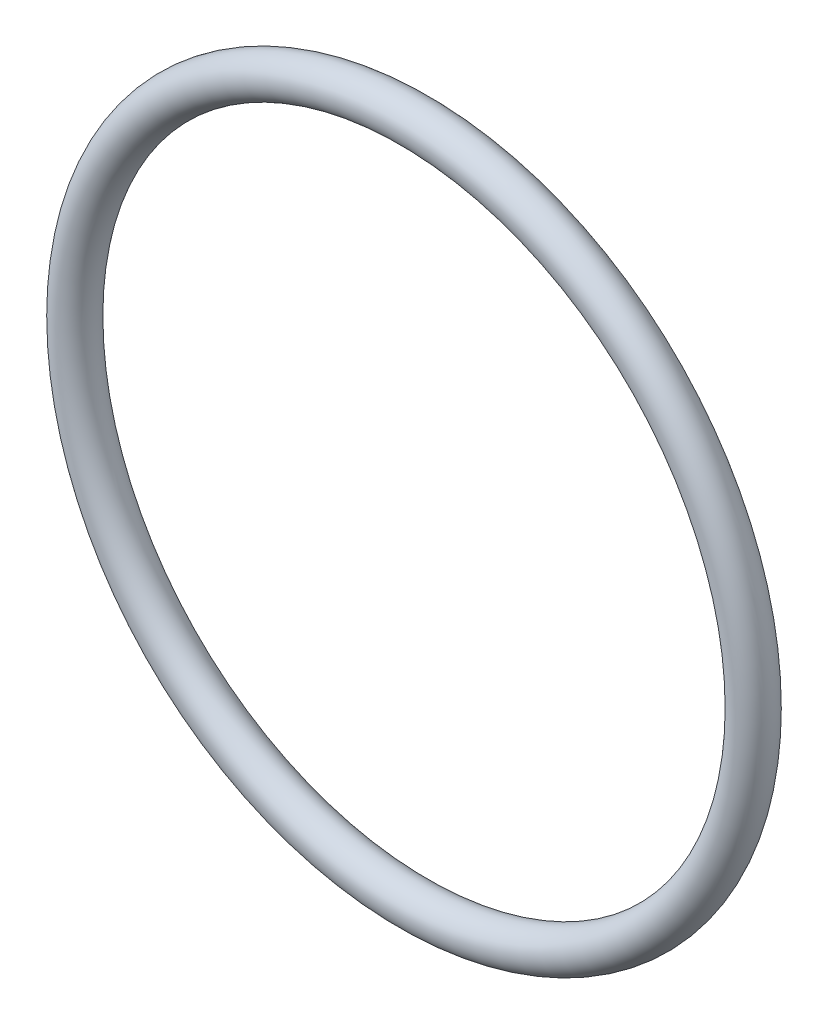
SolidWorks part; units mm, degrees
ref_plane "Front" through (0, 0, 0) normal (0, 0, 1) x (1, 0, 0)
ref_plane "Top" through (0, 0, 0) normal (0, 1, 0) x (1, 0, 0)
ref_plane "Right" through (0, 0, 0) normal (1, 0, 0) x (0, 0, -1)
sketch "Sketch1" plane through (0, 0, 0) normal (1, 0, 0) x (0, -1, 0)
  line L0 (0, -1.7653) -> (0, 1.7653) construction
  line L2 (-35.0926, 0) -> (35.0926, 0) construction
  line L3 (-28.3718, 0) -> (28.3718, 0) construction
  circle A0 centre (30.1371, 0) radius 1.7653
  point P9 (28.3718, 0)
  point P10 (31.9024, 0)
  point P13 (30.1371, 1.7653)
  point P14 (30.1371, -1.7653)
  dimension "Width" = 3.5306
  dimension "ID" = 56.7436
revolve "Revolve1" add sketch "Sketch1" angle 360 about L0
